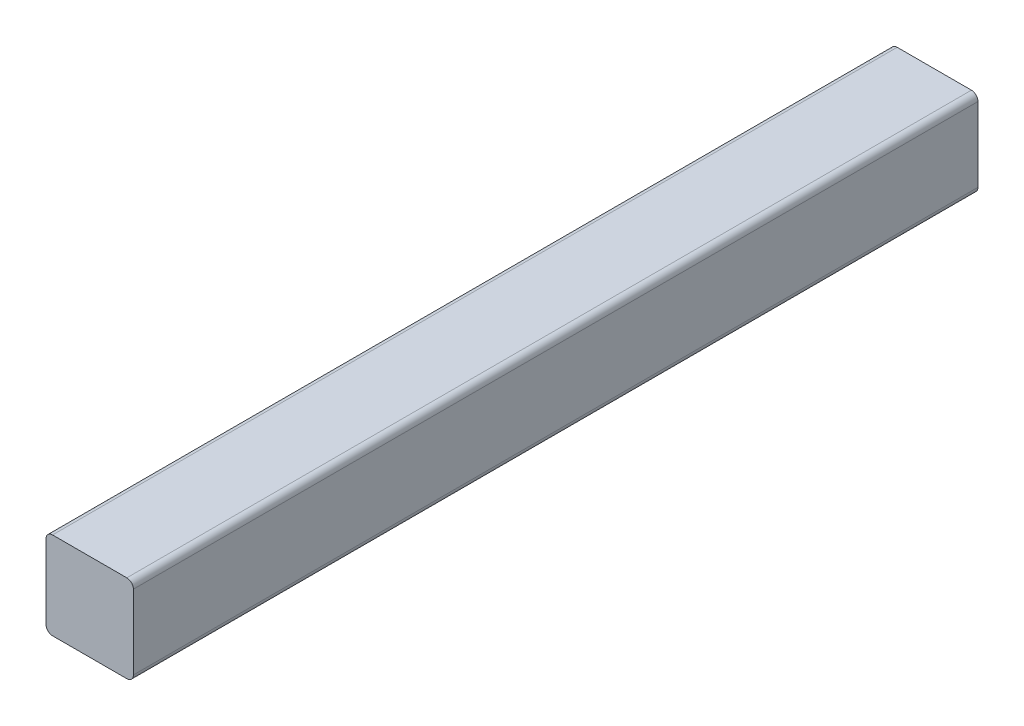
SolidWorks part; units mm, degrees
ref_plane "Plan de face" through (0, 0, 0) normal (0, 0, 1) x (1, 0, 0)
ref_plane "Plan de dessus" through (0, 0, 0) normal (0, 1, 0) x (1, 0, 0)
ref_plane "Plan de droite" through (0, 0, 0) normal (1, 0, 0) x (0, 0, -1)
sketch "Esquisse1" plane through (0, 0, 0) normal (0, 0, 1) x (1, 0, 0)
  line L0 (0, -63.3691) -> (0, 71.2902) construction
  line L1 (-75.6108, 0) -> (80.6515, 0) construction
  line L2 (-15, 12.75) -> (-15, -12.75)
  line L3 (-12.75, 15) -> (12.75, 15)
  line L4 (-12.75, -15) -> (12.75, -15)
  line L6 (15, 12.75) -> (15, -12.75)
  arc A0 (12.75, 15) -> (15, 12.75) centre (12.75, 12.75) cw
  arc A1 (-12.75, 15) -> (-15, 12.75) centre (-12.75, 12.75) ccw
  arc A2 (-12.75, -15) -> (-15, -12.75) centre (-12.75, -12.75) cw
  arc A3 (12.75, -15) -> (15, -12.75) centre (12.75, -12.75) ccw
  point P5 (-15, 0)
  point P14 (0, 15)
  point P20 (0, -15)
  point P21 (15, 0)
  dimension "D3" = 2.25
  dimension "D1" = 30
  dimension "D2" = 30
extrude "Extrusion1" add sketch "Esquisse1" along normal blind 290
